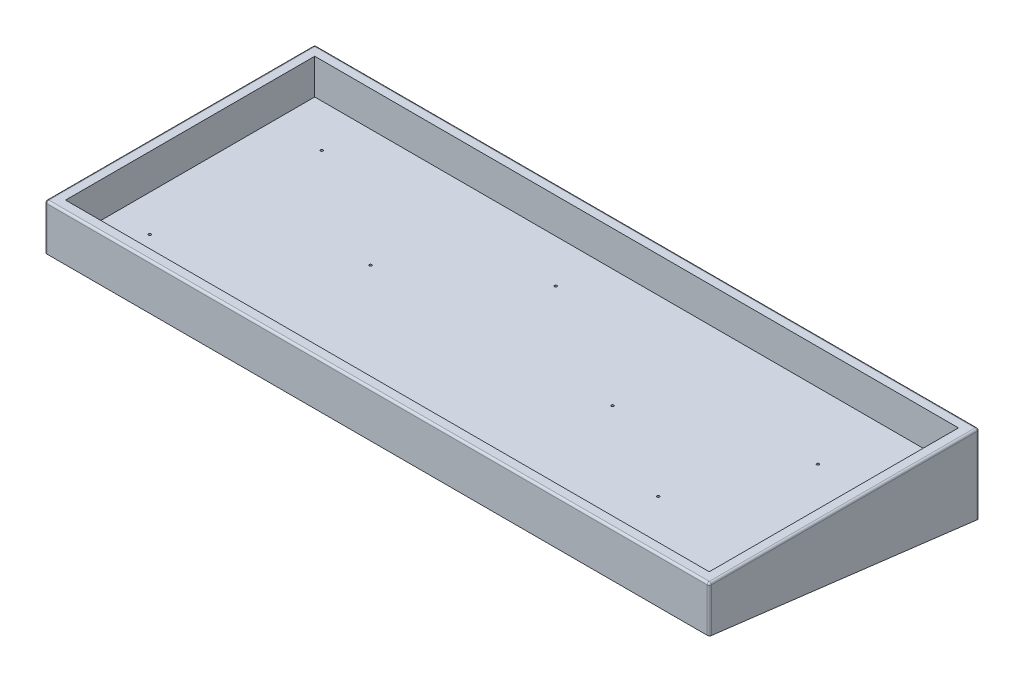
SolidWorks part; units mm, degrees
ref_plane "Front Plane" through (0, 0, 0) normal (0, 0, 1) x (1, 0, 0)
ref_plane "Top Plane" through (0, 0, 0) normal (0, 1, 0) x (1, 0, 0)
ref_plane "Right Plane" through (0, 0, 0) normal (1, 0, 0) x (0, 0, -1)
sketch "Sketch1" plane through (0, 0, 0) normal (0, 1, 0) x (1, 0, 0)
  line L1 (0, 0) -> (320, 0)
  line L2 (0, 0) -> (0, 130)
  line L3 (0, 130) -> (320, 130)
  line L4 (320, 0) -> (320, 130)
extrude "Boss-Extrude3" add sketch "Sketch1" along normal blind 22
sketch "Sketch3" plane through (0, 22, 0) normal (0, 1, 0) x (1, 0, 0)
  line L8 (5, 125) -> (5, 5)
  line L9 (5, 5) -> (315, 5)
  line L10 (315, 5) -> (315, 125)
  line L11 (315, 125) -> (5, 125)
  line L12 (5, 125) -> (5, 5)
  line L13 (5, 5) -> (315, 5)
  line L14 (315, 5) -> (315, 125)
  line L15 (315, 125) -> (5, 125)
  dimension "D1" = 5
extrude "Cut-Extrude1" cut sketch "Sketch3" against normal blind 17
draft "Draft1" type of draft neutral plane draft angle 7 faces to draft 1 face at (160, 0, -65) neutral plane through (0, 22, 0) neutral plane normal (0, 0, 1) parameters "D1"=7
fillet "Fillet2" radius 1 8 edges at (320, 3.019, -130) (320, 11, 0) (0, 3.019, -130) (0, 11, 0) (0, 22, -65) (160, 22, -130) (160, 22, 0) (320, 22, -65)
hole_wizard "#0-80 Tapped Hole1" positions "3DSketch2" profile "Sketch5" tap size "#0-80" standard "ANSI Inch" end condition through all
sketch3d "3DSketch2"
  point P3 (28.9711, 5, -104.4319)
  point P5 (141.9336, 5, -104.1307)
  point P7 (88.6153, 5, -68.2839)
  point P9 (205.4939, 5, -67.9827)
  point P11 (254.2937, 5, -41.1729)
  point P13 (279.296, 5, -92.985)
  point P15 (22.6452, 5, -27.9186)
  point P17 (168.1409, 5, -20.689)
sketch "Sketch5" plane through (28.9711, 5, -104.4319) normal (1, 0, 0) x (0, 0, 1)
  line L0 (0, 0) -> (0, 20.962)
  line L1 (0, 20.962) -> (0.5956, 20.962)
  line L2 (0.5956, 20.962) -> (0.5956, 0)
  line L5 (0.5956, 0) -> (0, 0)
  line L11 (0, -6.35) -> (0, 107.95) construction
  dimension "Thru Tap Drill Dia." = 1.1913
  dimension "Thru Tap Drill Depth" = 20.962
cosmetic thread "Hole Thread1" parameters "D2"=1.524
cosmetic thread "Hole Thread2" parameters "D2"=1.524
cosmetic thread "Hole Thread3" parameters "D2"=1.524
cosmetic thread "Hole Thread4" parameters "D2"=1.524
cosmetic thread "Hole Thread5" parameters "D2"=1.524
cosmetic thread "Hole Thread6" parameters "D2"=1.524
cosmetic thread "Hole Thread7" parameters "D2"=1.524
cosmetic thread "Hole Thread8" parameters "D2"=1.524
